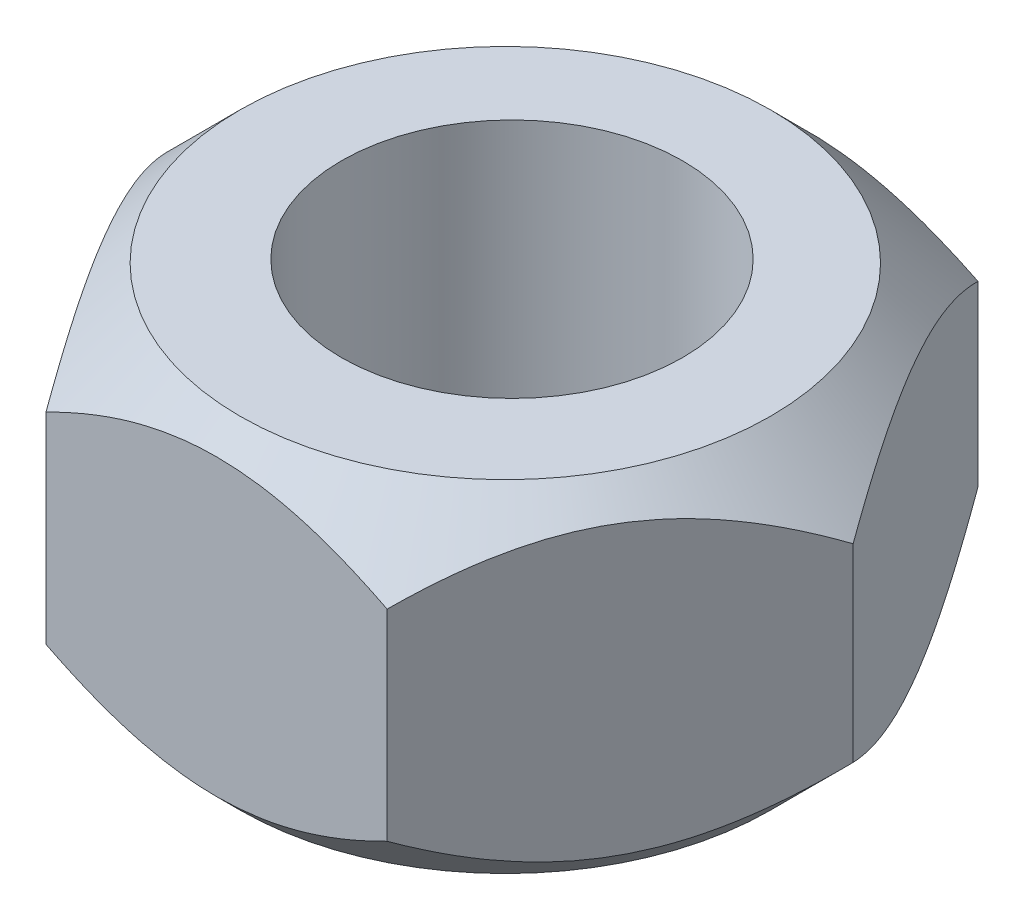
SolidWorks part; units mm, degrees
ref_plane "Front Plane" through (0, 0, 0) normal (0, 0, 1) x (1, 0, 0)
ref_plane "Top Plane" through (0, 0, 0) normal (0, 1, 0) x (1, 0, 0)
ref_plane "Right Plane" through (0, 0, 0) normal (1, 0, 0) x (0, 0, -1)
sketch "Sketch1" plane through (0, 0, 0) normal (0, 1, 0) x (1, 0, 0)
  line L1 (-4.5, -7.7942) -> (4.5, -7.7942)
  line L2 (4.5, -7.7942) -> (9, 0)
  line L3 (9, 0) -> (4.5, 7.7942)
  line L4 (4.5, 7.7942) -> (-4.5, 7.7942)
  line L5 (-4.5, 7.7942) -> (-9, 0)
  line L6 (-9, 0) -> (-4.5, -7.7942)
  circle A0 centre (0, 0) radius 7.7942 construction
  circle A1 centre (0, 0) radius 4.5
  dimension "D1" = 9
  dimension "D2" = 9
extrude "Boss-Extrude1" add sketch "Sketch1" along normal mid plane 9
sketch "Sketch2" plane through (0, 4.5, 0) normal (0, 1, 0) x (1, 0, 0)
  circle A0 centre (0, -0.1764) radius 7
  dimension "D1" = 14
extrude "Cut-Extrude2" cut sketch "Sketch2" against normal blind 9 draft 45 flip side to cut
mirror "Mirror4" about plane through (0, 0, 0) normal (0, 1, 0) of "Cut-Extrude2"
